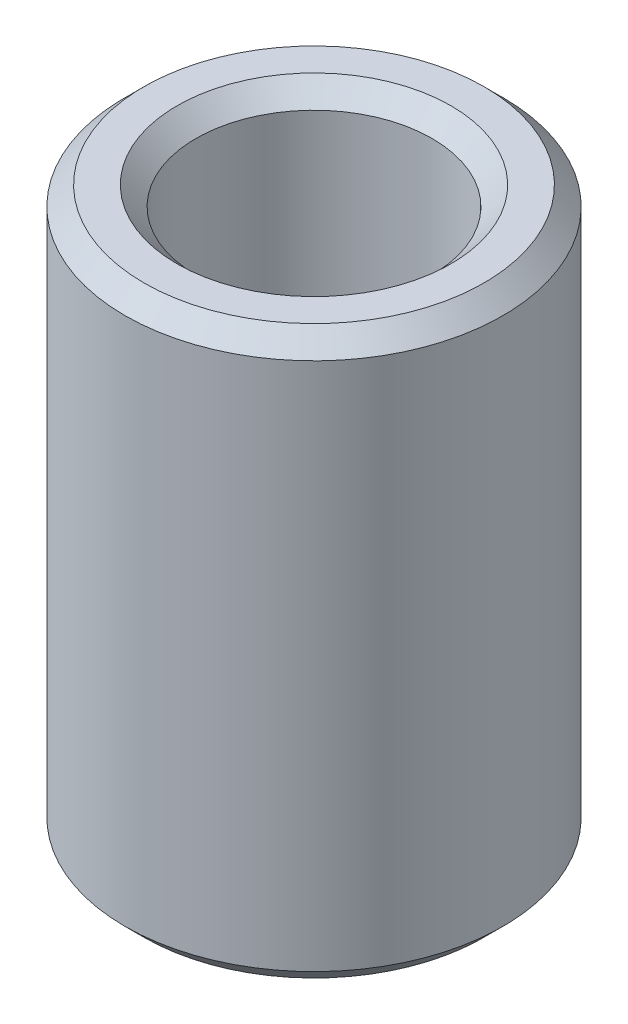
SolidWorks part; units mm, degrees
ref_plane "Front Plane" through (0, 0, 0) normal (0, 0, 1) x (1, 0, 0)
ref_plane "Top Plane" through (0, 0, 0) normal (0, 1, 0) x (1, 0, 0)
ref_plane "Right Plane" through (0, 0, 0) normal (1, 0, 0) x (0, 0, -1)
sketch "Sketch1" plane through (0, 0, 0) normal (0, 1, 0) x (1, 0, 0)
  circle A0 centre (0, 0) radius 20
  circle A1 centre (0, 0) radius 12.5
extrude "Boss-Extrude1" add sketch "Sketch1" along normal mid plane 60
chamfer "Chamfer1" distance 2 angle 45 1 edges at (0, 30, 20)
chamfer "Chamfer2" distance 2 angle 45 1 edges at (0, 30, 12.5)
chamfer "Chamfer3" distance 2 angle 45 1 edges at (0, -30, 20)
chamfer "Chamfer4" distance 2 angle 45 1 edges at (0, -30, 12.5)
